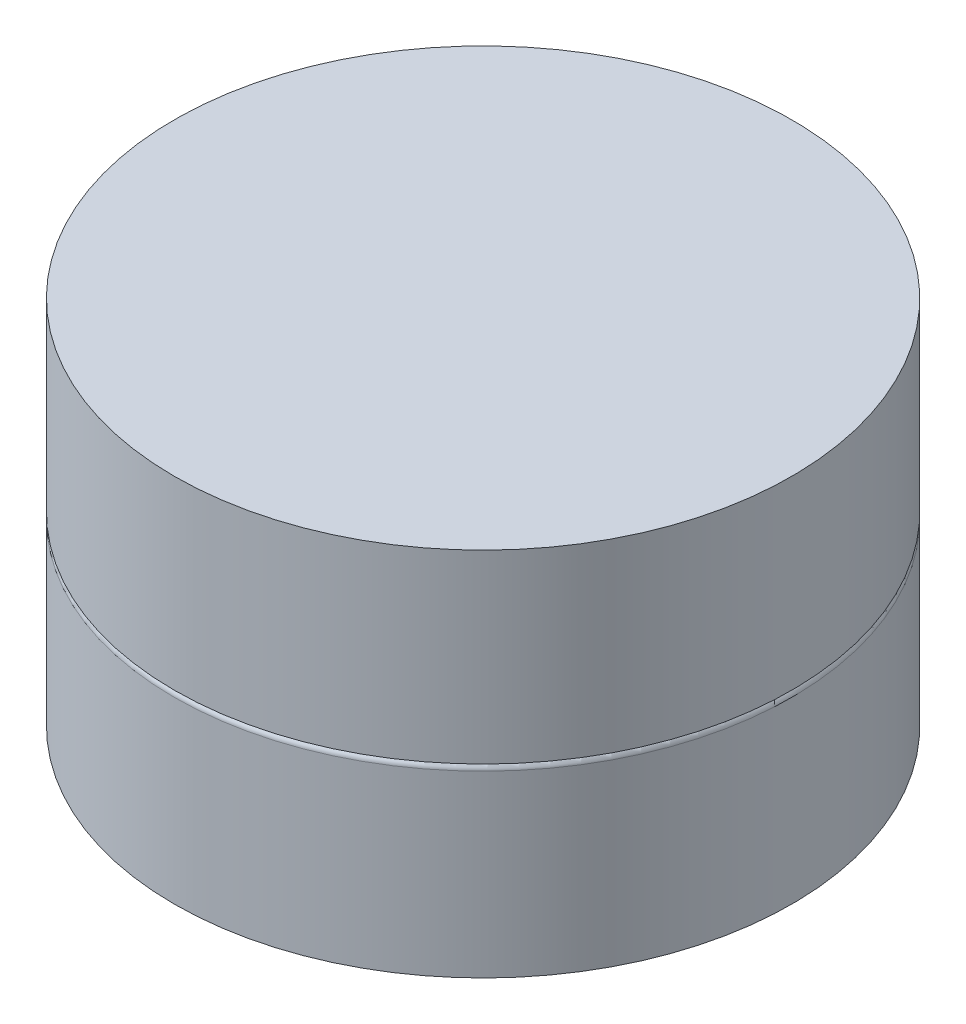
SolidWorks part; units mm, degrees
ref_plane "Front Plane" through (0, 0, 0) normal (0, 0, 1) x (1, 0, 0)
ref_plane "Top Plane" through (0, 0, 0) normal (0, 1, 0) x (1, 0, 0)
ref_plane "Right Plane" through (0, 0, 0) normal (1, 0, 0) x (0, 0, -1)
sketch "Sketch1" plane through (0, 0, 0) normal (0, 1, 0) x (1, 0, 0)
  circle A0 centre (0, 0) radius 2.5
  dimension "D1" = 5
extrude "Boss-Extrude1" add sketch "Sketch1" along normal blind 1.5
fillet "Fillet1" radius 0.05 1 edges at (0, 1.5, 2.5)
sketch "Sketch2" plane through (0, 1.5, 0) normal (0, 1, 0) x (1, 0, 0)
  circle A0 centre (0, 0) radius 2.5 construction
  circle A1 centre (0, 0) radius 2.5
extrude "Boss-Extrude2" add sketch "Sketch2" along normal blind 1.5
